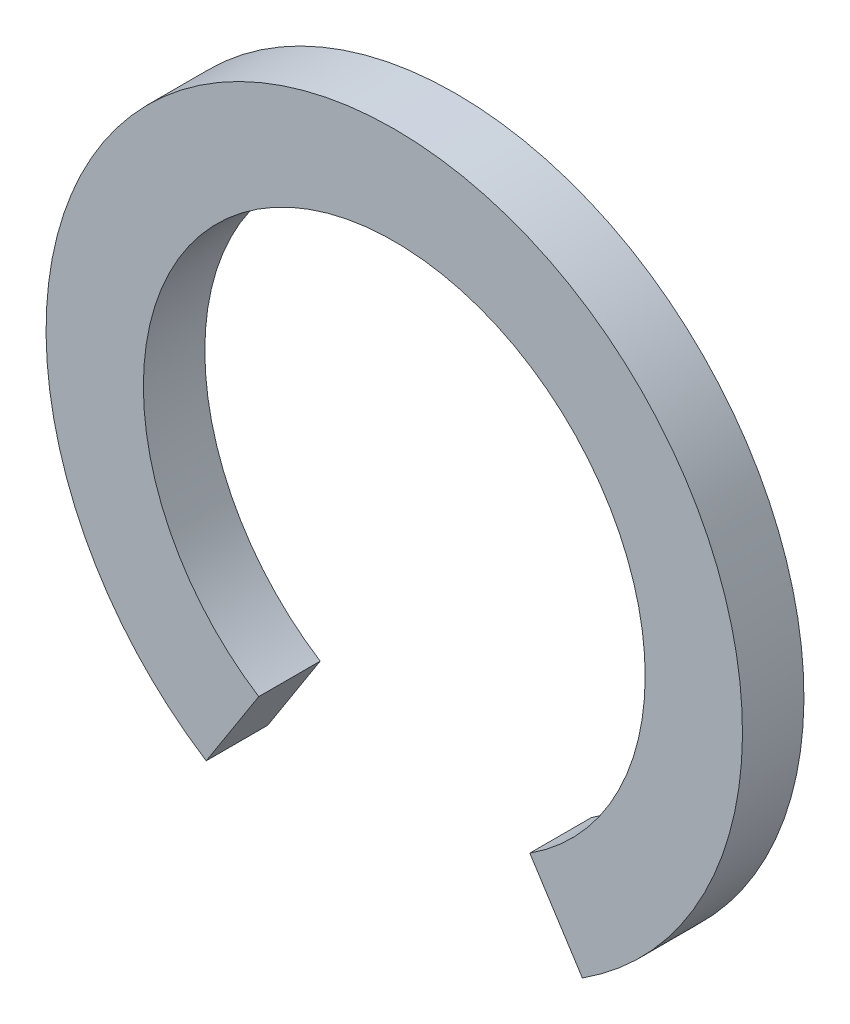
SolidWorks part; units mm, degrees
ref_plane "Front Plane" through (0, 0, 0) normal (0, 0, 1) x (1, 0, 0)
ref_plane "Top Plane" through (0, 0, 0) normal (0, 1, 0) x (1, 0, 0)
ref_plane "Right Plane" through (0, 0, 0) normal (1, 0, 0) x (0, 0, -1)
sketch "Sketch1" plane through (0, 0, 0) normal (0, 0, 1) x (1, 0, 0)
  line L0 (-3.3083, -5.1547) -> (-4.591, -7.1535)
  line L1 (0, -55) -> (0, 55) construction
  line L2 (3.3083, -5.1547) -> (4.591, -7.1535)
  arc A0 (3.3083, -5.1547) -> (-3.3083, -5.1547) centre (0, 0) ccw
  arc A1 (4.591, -7.1535) -> (-4.591, -7.1535) centre (0, 0) ccw
  dimension "D1" = 12.25
  dimension "D2" = 17
extrude "Boss-Extrude1" add sketch "Sketch1" along normal blind 1.5
